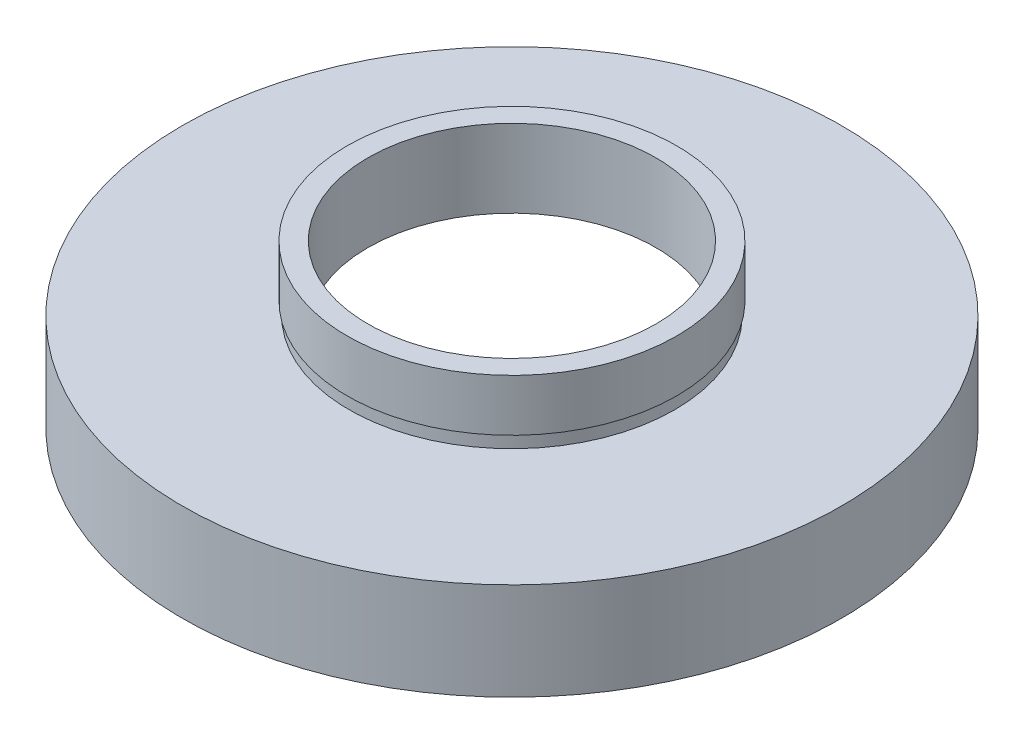
SolidWorks part; units mm, degrees
ref_plane "前视基准面" through (0, 0, 0) normal (0, 0, 1) x (1, 0, 0)
ref_plane "上视基准面" through (0, 0, 0) normal (0, 1, 0) x (1, 0, 0)
ref_plane "右视基准面" through (0, 0, 0) normal (1, 0, 0) x (0, 0, -1)
sketch "草图1" plane through (0, 0, 0) normal (0, 0, 1) x (1, 0, 0)
  line L0 (0, 16.886) -> (0, -24.4878) construction
  line L1 (20.5, 0) -> (20.5, 5.5)
  line L2 (11.1, 6.5) -> (21.1, 6.5)
  line L3 (11.1, 6.5) -> (11.1, 12.5)
  line L4 (11.1, 12.5) -> (12.7, 12.5)
  line L5 (12.7, 12.5) -> (12.7, 8.5)
  line L6 (12.7, 8.5) -> (12.55, 8.5)
  line L7 (12.55, 8.5) -> (12.55, 7.5)
  line L8 (12.55, 7.5) -> (25.4, 7.5)
  line L9 (25.4, 7.5) -> (25.4, 0)
  line L10 (25.4, 0) -> (20.5, 0)
  line L11 (20.5, 5.5) -> (21.1, 5.5)
  line L12 (21.1, 5.5) -> (21.1, 6.5)
  line L13 (0, 0) -> (3.4668, 0) construction
  point P4 (22.95, 0)
  dimension "D1" = 11.1
  dimension "D2" = 12.7
  dimension "D3" = 12.55
  dimension "D4" = 20.5
  dimension "D5" = 21.1
  dimension "D6" = 25.4
  dimension "D7" = 12.5
  dimension "D8" = 7.5
  dimension "D9" = 1
  dimension "D10" = 5.5
  dimension "D11" = 1
revolve "旋转1" add sketch "草图1" angle 360 about L0
cosmetic thread "装饰螺纹线1"
cosmetic thread "装饰螺纹线2"
cosmetic thread "装饰螺纹线3"
